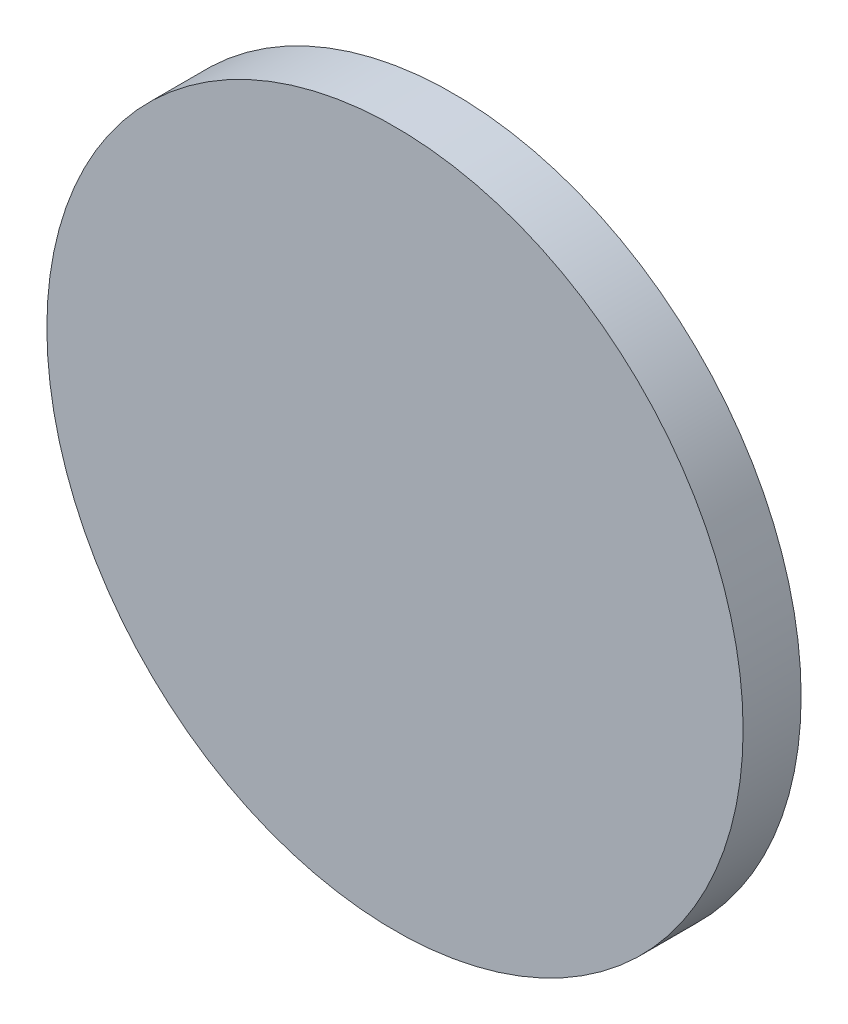
SolidWorks part; units mm, degrees
ref_plane "Front Plane" through (0, 0, 0) normal (0, 0, 1) x (1, 0, 0)
ref_plane "Top Plane" through (0, 0, 0) normal (0, 1, 0) x (1, 0, 0)
ref_plane "Right Plane" through (0, 0, 0) normal (1, 0, 0) x (0, 0, -1)
sketch "Sketch1" plane through (0, 0, 0) normal (0, 0, 1) x (1, 0, 0)
  circle A0 centre (0, 0) radius 6
  dimension "D1" = 12
extrude "Boss-Extrude1" add sketch "Sketch1" along normal blind 1
